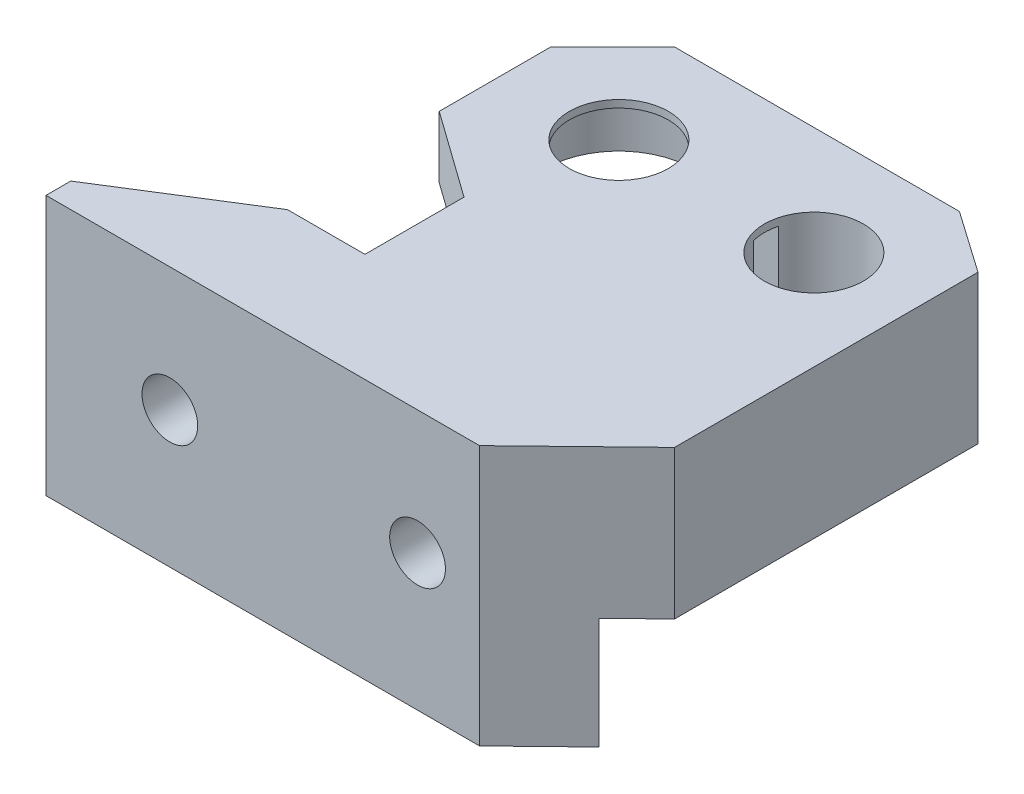
SolidWorks part; units mm, degrees
ref_plane "Front Plane" through (0, 0, 0) normal (0, 0, 1) x (1, 0, 0)
ref_plane "Top Plane" through (0, 0, 0) normal (0, 1, 0) x (1, 0, 0)
ref_plane "Right Plane" through (0, 0, 0) normal (1, 0, 0) x (0, 0, -1)
sketch "Sketch1" plane through (0, 0, 0) normal (0, 1, 0) x (1, 0, 0)
  line L0 (0, 0) -> (15.75, 0) construction
  line L5 (-4.25, 8.75) -> (18.75, 8.75)
  line L6 (18.75, 8.75) -> (23.75, 5.25)
  line L7 (23.75, 5.25) -> (23.75, -19.25)
  line L8 (23.75, -19.25) -> (15.75, -27)
  line L9 (15.75, -27) -> (-19.25, -27)
  line L10 (-19.25, -27) -> (-19.25, -25)
  line L11 (-19.25, -25) -> (-8.5, -18.25)
  line L12 (-8.5, -18.25) -> (-2.25, -18.25)
  line L13 (-2.25, -18.25) -> (-2.25, -10.25)
  line L14 (-2.25, -10.25) -> (-9.25, -5.25)
  line L15 (-9.25, -5.25) -> (-9.25, 3.75)
  line L16 (-9.25, 3.75) -> (-4.25, 8.75)
  line L17 (15.75, 0) -> (23.75, 0) construction
  circle A0 centre (0, 0) radius 4
  circle A1 centre (15.75, 0) radius 4
  point P0 (0, 0)
  dimension "D2" = 8
  dimension "D3" = 8
  dimension "D1" = 15.75
  dimension "D4" = 23
  dimension "D5" = 5
  dimension "D6" = 3.5
  dimension "D7" = 24.5
  dimension "D8" = 8
  dimension "D9" = 8.75
  dimension "D10" = 5
  dimension "D11" = 5
  dimension "D12" = 7
  dimension "D13" = 5
  dimension "D14" = 9
  dimension "D15" = 8
  dimension "D16" = 7.75
  dimension "D17" = 35
  dimension "D18" = 6.25
  dimension "D19" = 6.75
  dimension "D20" = 2
extrude "Boss-Extrude1" add sketch "Sketch1" along normal blind 5
sketch "Sketch2" plane through (0, 0, 0) normal (0, -1, 0) x (1, 0, 0)
  line L0 (23.75, 19.25) -> (23.75, -5.25)
  line L1 (23.75, -5.25) -> (20.25, -5.25)
  line L2 (20.25, -5.25) -> (20.25, 18.25)
  line L3 (20.25, 18.25) -> (-8.5, 18.25)
  line L4 (-8.5, 18.25) -> (-14.8704, 22.25)
  line L5 (-8.5, 18.25) -> (-19.25, 25) construction
  line L6 (-14.8704, 22.25) -> (20.6532, 22.25)
  line L7 (15.75, 27) -> (23.75, 19.25) construction
  line L8 (20.6532, 22.25) -> (23.75, 19.25)
  dimension "D1" = 3.5
  dimension "D2" = 4
extrude "Boss-Extrude2" add sketch "Sketch2" along normal blind 7
sketch "Sketch3" plane through (0, 0, 0) normal (0, -1, 0) x (1, 0, 0)
  line L5 (-14.8704, 22.25) -> (20.6532, 22.25)
  line L6 (20.6532, 22.25) -> (15.75, 27)
  line L7 (15.75, 27) -> (-19.25, 27)
  line L8 (-19.25, 27) -> (-19.25, 25)
  line L9 (-19.25, 25) -> (-14.8704, 22.25)
  line L10 (-14.8704, 22.25) -> (20.6532, 22.25)
  line L11 (20.6532, 22.25) -> (15.75, 27)
  line L12 (15.75, 27) -> (-19.25, 27)
  line L13 (-19.25, 27) -> (-19.25, 25)
  line L14 (-19.25, 25) -> (-14.8704, 22.25)
  dimension "D1" = 0
extrude "Boss-Extrude3" add sketch "Sketch3" along normal blind 16
sketch "Sketch6" plane through (0, 0, 0) normal (0, -1, 0) x (1, 0, 0)
  circle A0 centre (15.75, 0) radius 7
  circle A1 centre (15.75, 0) radius 4
  dimension "D1" = 14
extrude "Boss-Extrude4" add sketch "Sketch6" along normal blind 2.5
sketch "Sketch4" plane through (0, 0, 0) normal (0, -1, 0) x (1, 0, 0)
  line L0 (0, 0) -> (12.25, 0) construction
  line L1 (5.8838, -1) -> (12.3959, -1)
  line L2 (5.8838, 1) -> (12.3959, 1)
  line L3 (0, -1) -> (15.75, -1) construction
  line L4 (0, 1) -> (15.75, 1) construction
  line L5 (0, 0) -> (15.75, 0) construction
  arc A0 (5.8838, 1) -> (5.8838, -1) centre (0, 0) ccw
  arc A2 (12.3959, 1) -> (12.3959, -1) centre (15.75, 0) ccw
  dimension "D1" = 1
  dimension "D2" = 1
extrude "Cut-Extrude1" cut sketch "Sketch4" against normal blind 4.4
sketch "Sketch7" plane through (0, 4.4, 0) normal (0, -1, 0) x (1, 0, 0)
  line L2 (5.8838, -1) -> (11.877, -1)
  line L3 (11.877, 1) -> (5.8838, 1)
  line L4 (5.8838, -1) -> (11.877, -1)
  line L5 (11.877, 1) -> (5.8838, 1)
  arc A2 (5.8838, 1) -> (5.8838, -1) centre (0, 0) ccw
  arc A3 (11.877, 1) -> (11.877, -1) centre (15.75, 0) ccw
  arc A4 (5.8838, 1) -> (5.8838, -1) centre (0, 0) ccw
  arc A5 (11.877, 1) -> (11.877, -1) centre (15.75, 0) ccw
  dimension "D1" = 0
extrude "Cut-Extrude2" cut sketch "Sketch7" along normal through all
sketch "Sketch8" plane through (0, 0, 27) normal (0, 0, 1) x (1, 0, 0)
  line L0 (10.75, -5) -> (-9.25, -5) construction
  line L1 (-19.25, 5) -> (15.75, 5) construction
  line L2 (-19.25, 5) -> (-19.25, -16) construction
  circle A0 centre (10.75, -5) radius 2.25
  circle A1 centre (-9.25, -5) radius 2.25
  dimension "D1" = 4.5
  dimension "D2" = 4.5
  dimension "D3" = 20
  dimension "D4" = 10
  dimension "D5" = 10
extrude "Cut-Extrude3" cut sketch "Sketch8" against normal through all
sketch "Sketch9" plane through (0, 0, 18.25) normal (0, 0, -1) x (-1, 0, 0)
  circle A0 centre (-10.75, -5) radius 4
  circle A1 centre (9.25, -5) radius 4
  dimension "D1" = 8
  dimension "D2" = 8
extrude "Cut-Extrude4" cut sketch "Sketch9" against normal blind 4
